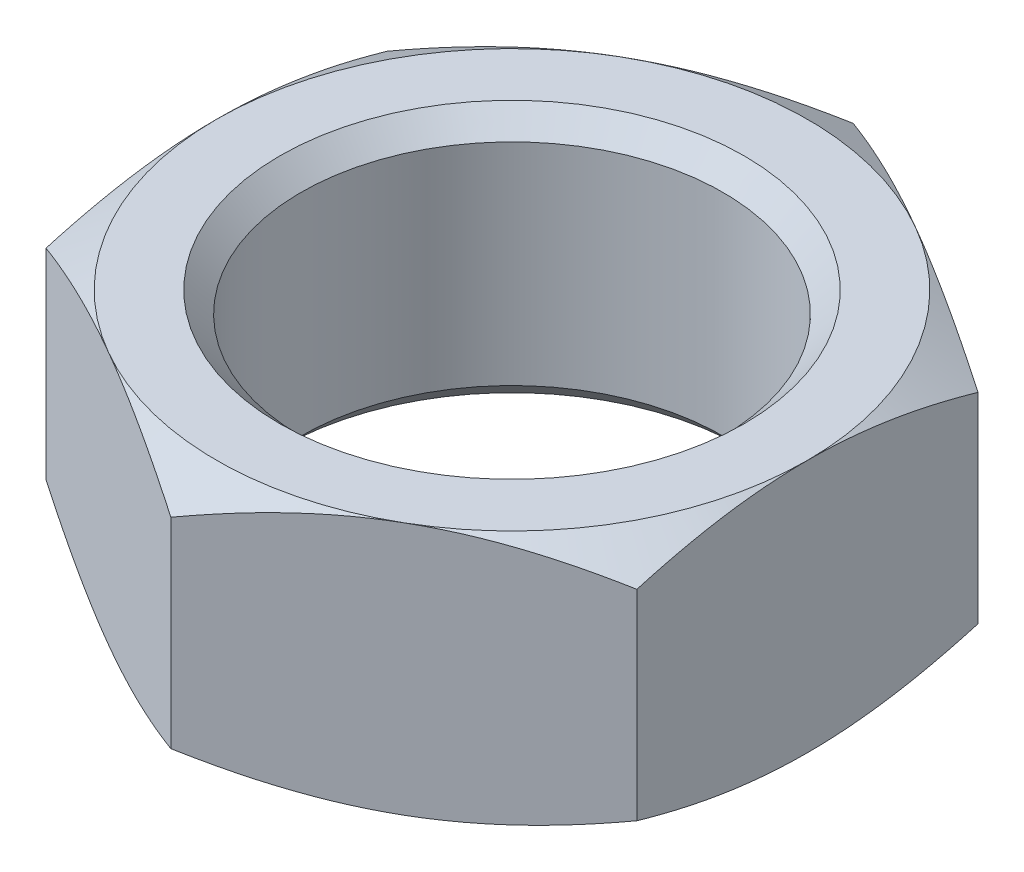
SolidWorks part; units mm, degrees
ref_plane "Front Plane" through (0, 0, 0) normal (0, 0, 1) x (1, 0, 0)
ref_plane "Top Plane" through (0, 0, 0) normal (0, 1, 0) x (1, 0, 0)
ref_plane "Right Plane" through (0, 0, 0) normal (1, 0, 0) x (0, 0, -1)
sketch "Sketch1" plane through (0, 0, 0) normal (0, 1, 0) x (1, 0, 0)
  line L1 (0, 16.1658) -> (-14, 8.0829)
  line L2 (-14, 8.0829) -> (-14, -8.0829)
  line L3 (-14, -8.0829) -> (0, -16.1658)
  line L4 (0, -16.1658) -> (14, -8.0829)
  line L5 (14, -8.0829) -> (14, 8.0829)
  line L6 (14, 8.0829) -> (0, 16.1658)
  circle A0 centre (0, 0) radius 14 construction
  dimension "D1" = 28
extrude "Boss-Extrude1" add sketch "Sketch1" along normal mid plane 12
sketch "Sketch2" plane through (0, 6, 0) normal (0, 1, 0) x (1, 0, 0)
  line L0 (14, 8.0829) -> (0, 16.1658) construction
  circle A0 centre (0, 0) radius 14
extrude "Cut-Extrude1" cut sketch "Sketch2" against normal blind 12 draft 60 flip side to cut
mirror "Mirror1" about plane through (0, 0, 0) normal (0, 1, 0) of "Cut-Extrude1"
sketch "Sketch3" plane through (0, 6, 0) normal (0, 1, 0) x (1, 0, 0)
  circle A0 centre (0, 0) radius 10
  dimension "D1" = 20
extrude "Cut-Extrude2" cut sketch "Sketch3" against normal through all
chamfer "Chamfer1" distance 1 angle 45 2 edges at (0, -6, 10) (0, 6, 10)
